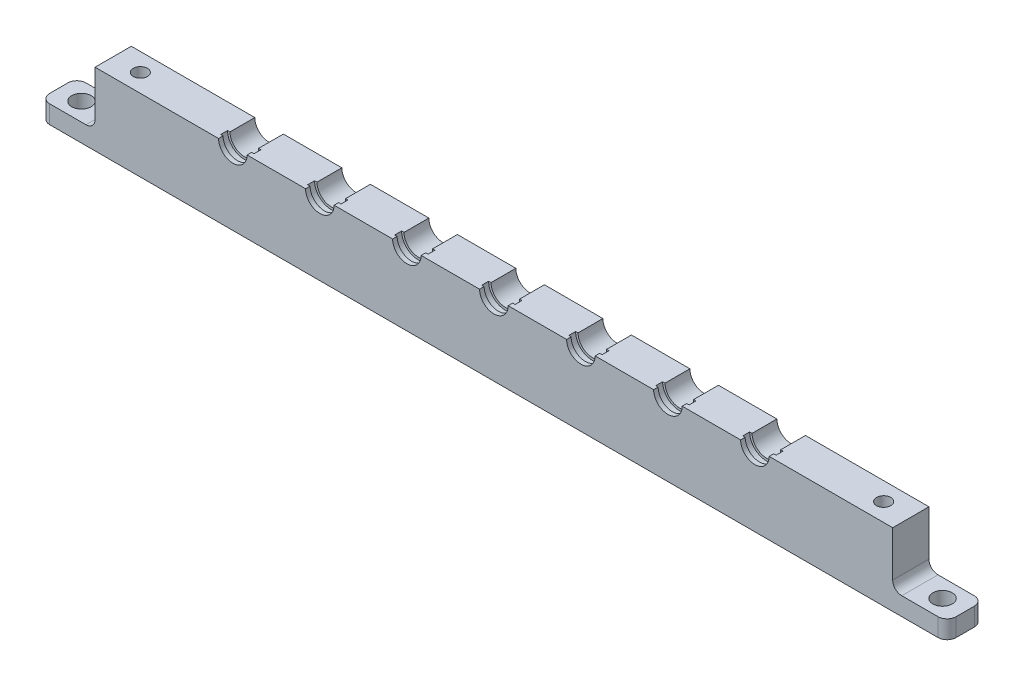
SolidWorks part; units mm, degrees
ref_plane "Front Plane" through (0, 0, 0) normal (0, 0, 1) x (1, 0, 0)
ref_plane "Top Plane" through (0, 0, 0) normal (0, 1, 0) x (1, 0, 0)
ref_plane "Right Plane" through (0, 0, 0) normal (1, 0, 0) x (0, 0, -1)
sketch "Sketch1" plane through (0, 0, 0) normal (0, 0, 1) x (1, 0, 0)
  line L1 (69.85, -6.35) -> (-69.85, -6.35)
  line L2 (69.85, -6.35) -> (69.85, 6.35)
  line L3 (69.85, 6.35) -> (-69.85, 6.35)
  line L4 (-69.85, -6.35) -> (-69.85, 6.35)
  line L5 (69.85, -6.35) -> (-69.85, 6.35) construction
  line L6 (69.85, 6.35) -> (-69.85, -6.35) construction
  point P0 (0, 0)
  dimension "D1" = 139.7
  dimension "D2" = 12.7
extrude "Boss-Extrude1" add sketch "Sketch1" along normal blind 6.35
hole_wizard "Tap Drill for M3x0.5 Tap1" positions "Sketch3" profile "Sketch4" hole size "M3x0.5" standard "ANSI Metric" end condition through all
sketch "Sketch3" plane through (0, 6.35, 0) normal (0, 1, 0) x (1, 0, 0)
  point P0 (-65.0875, -3.175)
  point P3 (65.0875, -3.175)
sketch "Sketch4" plane through (-65.0875, 6.35, 3.175) normal (1, 0, 0) x (0, 0, 1)
  line L0 (0, 0) -> (0, 12.7)
  line L1 (0, 12.7) -> (1.25, 12.7)
  line L2 (1.25, 12.7) -> (1.25, 0)
  line L5 (1.25, 0) -> (0, 0)
  line L11 (0, -6.35) -> (0, 107.95) construction
  dimension "Thru Hole Dia." = 2.5
  dimension "Thru Hole Depth" = 12.7
sketch "Sketch5" plane through (0, -6.35, 0) normal (0, -1, 0) x (1, 0, 0)
  line L0 (-69.85, 0) -> (69.85, 0) construction
  line L1 (-69.85, 6.35) -> (-79.375, 6.35)
  line L2 (-69.85, 6.35) -> (-69.85, 0)
  line L3 (-69.85, 0) -> (-79.375, 0)
  line L4 (-79.375, 6.35) -> (-79.375, 0)
  dimension "D1" = 9.525
extrude "Boss-Extrude2" add sketch "Sketch5" against normal blind 3.175
fillet "Fillet1" radius 1.5875 1 edges at (-69.85, -3.175, 3.175)
hole_wizard "M3 Clearance Hole1" positions "Sketch6" profile "Sketch7" hole size "M3" standard "ANSI Metric" end condition through all
sketch "Sketch6" plane through (0, -3.175, 0) normal (0, 1, 0) x (1, 0, 0)
  line L0 (-75.4062, 0) -> (-75.4062, -6.35) construction
  line L1 (-79.375, 0) -> (-71.4375, 0) construction
  line L2 (-71.4375, -6.35) -> (-79.375, -6.35) construction
  point P9 (-75.4062, -3.175)
sketch "Sketch7" plane through (-75.4062, -3.175, 3.175) normal (1, 0, 0) x (0, 0, 1)
  line L0 (0, 0) -> (0, 3.175)
  line L1 (0, 3.175) -> (1.7, 3.175)
  line L2 (1.7, 3.175) -> (1.7, 0)
  line L5 (1.7, 0) -> (0, 0)
  line L11 (0, -6.35) -> (0, 107.95) construction
  dimension "Thru Hole Dia." = 3.4
  dimension "Thru Hole Depth" = 3.175
fillet "Fillet2" radius 1.5875 2 edges at (-79.375, -4.7625, 0) (-79.375, -4.7625, 6.35)
mirror "Mirror5" about plane through (0, 0, 0) normal (1, 0, 0) of "Fillet2", "M3 Clearance Hole1", "Boss-Extrude2"
fillet "Fillet3" radius 1.5875 1 edges at (69.85, -3.175, 3.175)
sketch "Sketch14" plane through (0, 0, 6.35) normal (0, 0, 1) x (1, 0, 0)
  line L0 (0, -6.35) -> (0, 6.35) construction
  line L1 (-77.7875, -6.35) -> (77.7875, -6.35) construction
  line L2 (69.85, 6.35) -> (-69.85, 6.35) construction
  circle A0 centre (0, 6.35) radius 2.5
  dimension "D1" = 5
extrude "Cut-Extrude2" cut sketch "Sketch14" against normal blind 0.7937
sketch "Sketch15" plane through (0, 0, 5.5562) normal (0, 0, 1) x (1, 0, 0)
  line L0 (2.5, 6.35) -> (-2.5, 6.35) construction
  circle A0 centre (0, 6.35) radius 2.921
  dimension "D1" = 5.842
extrude "Cut-Extrude3" cut sketch "Sketch15" against normal blind 1.2065
sketch "Sketch16" plane through (0, 0, 4.3497) normal (0, 0, 1) x (1, 0, 0)
  arc A0 (-2.5, 6.35) -> (2.5, 6.35) centre (0, 6.35) ccw construction
  arc A1 (-2.5, 6.35) -> (2.5, 6.35) centre (0, 6.35) ccw
extrude "Cut-Extrude4" cut sketch "Sketch16" against normal through all and the other way through all
pattern_linear "LPattern1" count 4 spacing 15.24 along (1, 0, 0) of "Cut-Extrude4", "Cut-Extrude3", "Cut-Extrude2"
pattern_linear "LPattern2" count 4 spacing 15.24 along (-1, 0, 0) of "Cut-Extrude4", "Cut-Extrude3", "Cut-Extrude2"
